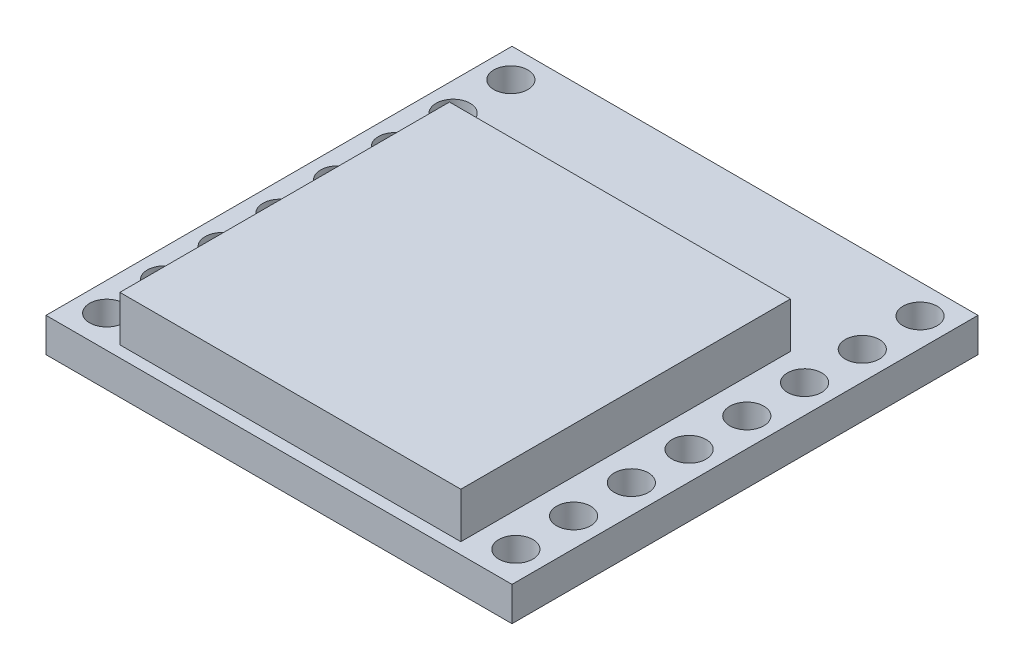
SolidWorks part; units mm, degrees
ref_plane "Front Plane" through (0, 0, 0) normal (0, 0, 1) x (1, 0, 0)
ref_plane "Top Plane" through (0, 0, 0) normal (0, 1, 0) x (1, 0, 0)
ref_plane "Right Plane" through (0, 0, 0) normal (1, 0, 0) x (0, 0, -1)
sketch "Sketch1" plane through (0, 0, 0) normal (0, 1, 0) x (1, 0, 0)
  line L1 (-10.25, -10.25) -> (10.25, -10.25)
  line L2 (-10.25, -10.25) -> (-10.25, 10.25)
  line L3 (-10.25, 10.25) -> (10.25, 10.25)
  line L4 (10.25, -10.25) -> (10.25, 10.25)
  line L5 (-10.25, -10.25) -> (10.25, 10.25) construction
  line L6 (-10.25, 10.25) -> (10.25, -10.25) construction
  point P0 (0, 0)
  dimension "D1" = 20.5
  dimension "D2" = 20.5
extrude "Boss-Extrude1" add sketch "Sketch1" along normal blind 1.5
sketch "Sketch2" plane through (0, 0, 0) normal (0, 1, 0) x (1, 0, 0)
  line L0 (0, -13.6862) -> (0, 20.8369) construction
  line L2 (10.25, 10.25) -> (-10.25, 10.25) construction
  circle A0 centre (-9, 8.95) radius 0.75
  circle A1 centre (-9, 6.41) radius 0.75
  circle A2 centre (-9, 3.87) radius 0.75
  circle A3 centre (-9, 1.33) radius 0.75
  circle A4 centre (-9, -1.21) radius 0.75
  circle A5 centre (-9, -3.75) radius 0.75
  circle A6 centre (-9, -6.29) radius 0.75
  circle A7 centre (-9, -8.83) radius 0.75
  circle A8 centre (9, -8.83) radius 0.75
  circle A9 centre (9, -6.29) radius 0.75
  circle A10 centre (9, -3.75) radius 0.75
  circle A11 centre (9, -1.21) radius 0.75
  circle A12 centre (9, 1.33) radius 0.75
  circle A13 centre (9, 3.87) radius 0.75
  circle A14 centre (9, 6.41) radius 0.75
  circle A15 centre (9, 8.95) radius 0.75
  dimension "D3" = 1.5
  dimension "D1" = 9
  dimension "D2" = 1.3
  dimension "D4" = 8
extrude "Cut-Extrude1" cut sketch "Sketch2" against normal through all from surface at 1.5 starting at face at (0, 1.5, 0)
sketch "Sketch3" plane through (0, 0, 0) normal (0, 1, 0) x (1, 0, 0)
  line L1 (-7.5, -9.75) -> (7.5, -9.75)
  line L2 (-7.5, -9.75) -> (-7.5, 4.75)
  line L3 (-7.5, 4.75) -> (7.5, 4.75)
  line L4 (7.5, -9.75) -> (7.5, 4.75)
  line L5 (-7.5, -9.75) -> (7.5, 4.75) construction
  line L6 (-7.5, 4.75) -> (7.5, -9.75) construction
  line L7 (10.25, 10.25) -> (-10.25, 10.25) construction
  point P0 (0, -2.5)
  dimension "D1" = 14.5
  dimension "D2" = 15
  dimension "D3" = 5.5
extrude "Boss-Extrude2" add sketch "Sketch3" along normal blind 2 from surface at 1.5 starting at face at (-9, 1.5, -7.16)
